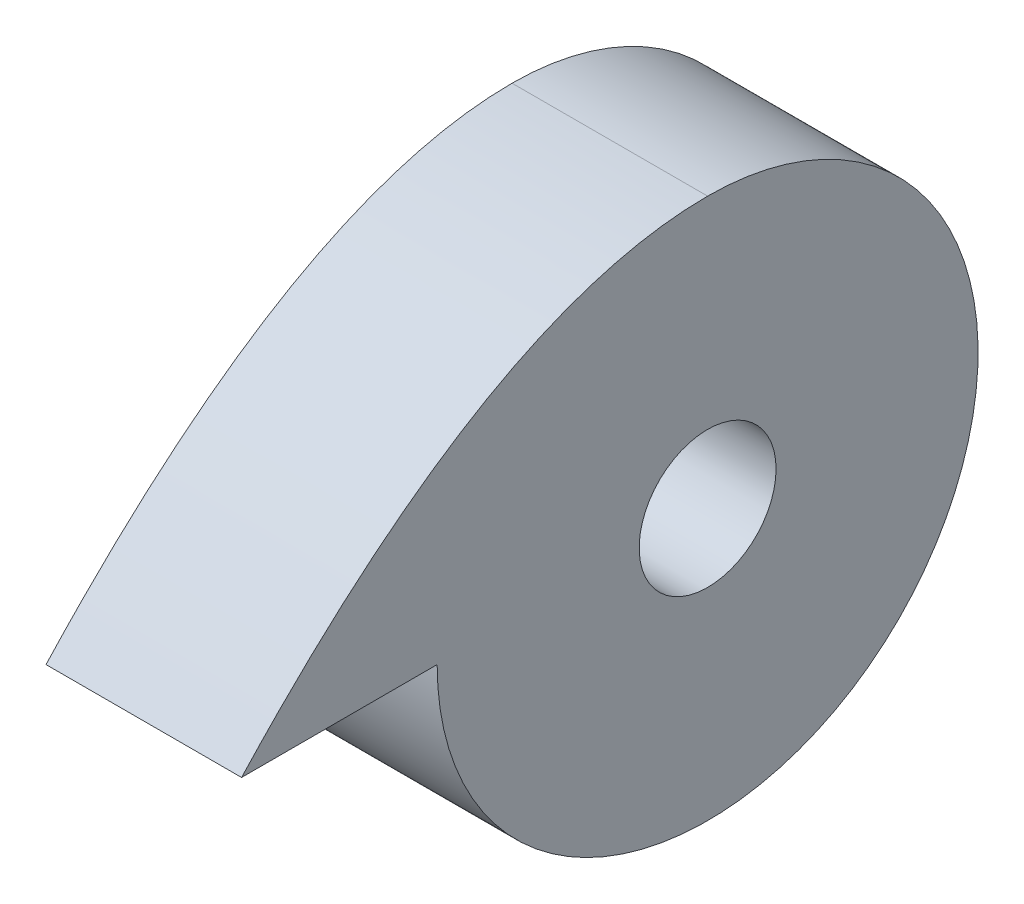
SolidWorks part; units mm, degrees
ref_plane "Front Plane" through (0, 0, 0) normal (0, 0, 1) x (1, 0, 0)
ref_plane "Top Plane" through (0, 0, 0) normal (0, 1, 0) x (1, 0, 0)
ref_plane "Right Plane" through (0, 0, 0) normal (1, 0, 0) x (0, 0, -1)
sketch "Sketch1" plane through (0, 0, 0) normal (1, 0, 0) x (0, 0, -1)
  line L0 (-47.9351, 7.4467) -> (-57.9351, 7.4467)
  line L1 (-42.9471, 21.276) -> (-25.2644, 21.276) construction
  arc A0 (-47.9351, 7.4467) -> (-34.1058, 21.276) centre (-34.1058, 7.4467) ccw
  spline S0 degree 2 poles (-34.1058, 21.276) (-45.1575, 21.276) (-57.9351, 7.4467) knots 0 0 0 1 1 1
  point P1 (-57.9351, 7.4467)
  dimension "D1" = 10
extrude "Boss-Extrude1" add sketch "Sketch1" along normal blind 10
hole_wizard "Tap Drill for M8x1.0 Tap1" positions "Sketch2" profile "Sketch3" hole size "M8x1.0" standard "ANSI Metric" end condition through all
sketch "Sketch2" plane through (10, 0, 0) normal (1, 0, 0) x (0, 0, -1)
  line L0 (-34.1058, 7.4467) -> (-34.1058, 21.276) construction
  point P0 (-34.1058, 7.4467)
  point P11 (-34.1058, 7.4467)
sketch "Sketch3" plane through (10, 7.4467, 34.1058) normal (0, 1, 0) x (0, 0, -1)
  line L0 (0, 0) -> (0, 10)
  line L1 (0, 10) -> (3.5, 10)
  line L2 (3.5, 10) -> (3.5, 0)
  line L5 (3.5, 0) -> (0, 0)
  line L11 (0, -6.35) -> (0, 107.95) construction
  dimension "Thru Hole Dia." = 7
  dimension "Thru Hole Depth" = 10
